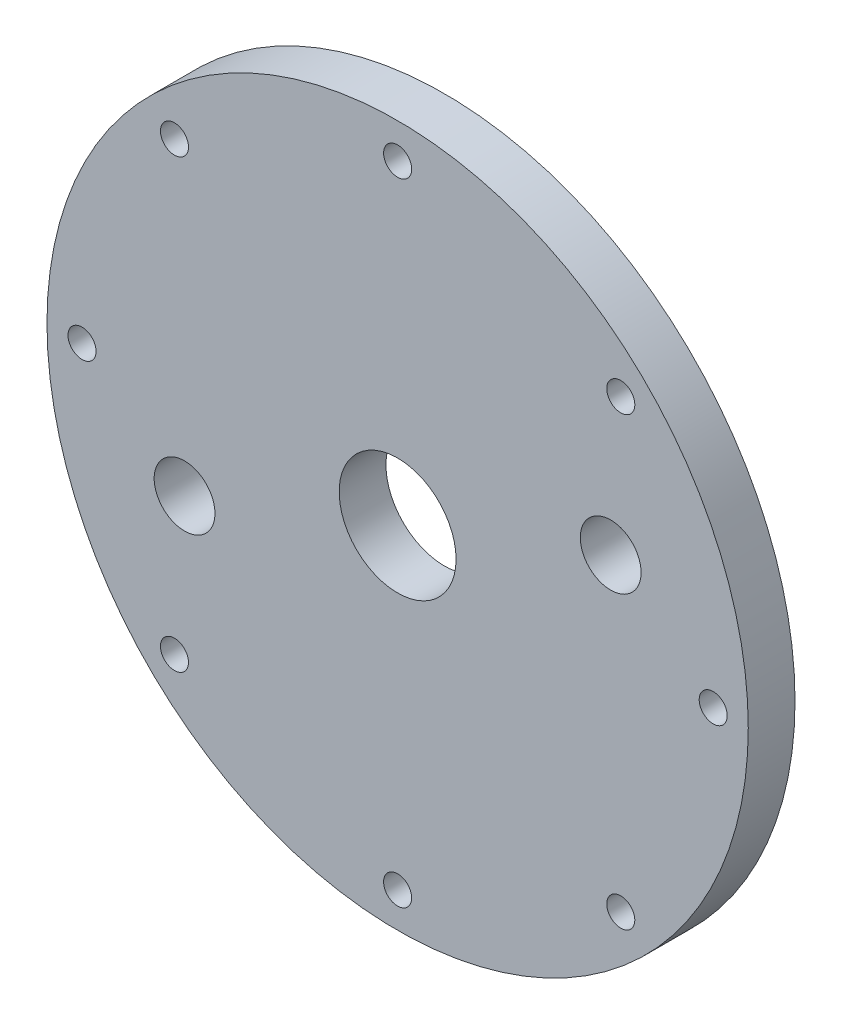
SolidWorks part; units mm, degrees
ref_plane "Alzado" through (0, 0, 0) normal (0, 0, 1) x (1, 0, 0)
ref_plane "Planta" through (0, 0, 0) normal (0, 1, 0) x (1, 0, 0)
ref_plane "Vista lateral" through (0, 0, 0) normal (1, 0, 0) x (0, 0, -1)
sketch "Croquis1" plane through (0, 0, 0) normal (0, 0, 1) x (1, 0, 0)
  circle A0 centre (0, 0) radius 75
  circle A1 centre (0, 0) radius 67.5 construction
  circle A2 centre (0, 67.5) radius 3
  circle A3 centre (47.7297, 47.7297) radius 3
  circle A4 centre (67.5, 0) radius 3
  circle A5 centre (47.7297, -47.7297) radius 3
  circle A6 centre (0, -67.5) radius 3
  circle A7 centre (-47.7297, -47.7297) radius 3
  circle A8 centre (-67.5, 0) radius 3
  circle A9 centre (-47.7297, 47.7297) radius 3
  circle A10 centre (0, 0) radius 12.5
  point P22 (0, 0)
  dimension "D1" = 135
  dimension "D2" = 150
  dimension "D3" = 6
  dimension "D5" = 25
  dimension "D4" = 8
extrude "Saliente-Extruir1" add sketch "Croquis1" along normal blind 10
sketch "Croquis2" plane through (0, 0, 10) normal (0, 0, 1) x (1, 0, 0)
  line L0 (45.5709, 17.3164) -> (-45.5709, -17.3164) construction
  line L1 (47.7297, 47.7297) -> (67.5, 0) construction
  circle A0 centre (0, 0) radius 48.75 construction
  circle A1 centre (45.5709, 17.3164) radius 6.5
  circle A2 centre (-45.5709, -17.3164) radius 6.5
  point P6 (0, 0)
  point P12 (0, 0)
  point P13 (0, 0)
  dimension "D1" = 97.5
  dimension "D2" = 13
  dimension "D3" = 13
  dimension "D4" = 17.3164
extrude "Cortar-Extruir1" cut sketch "Croquis2" against normal blind 10
